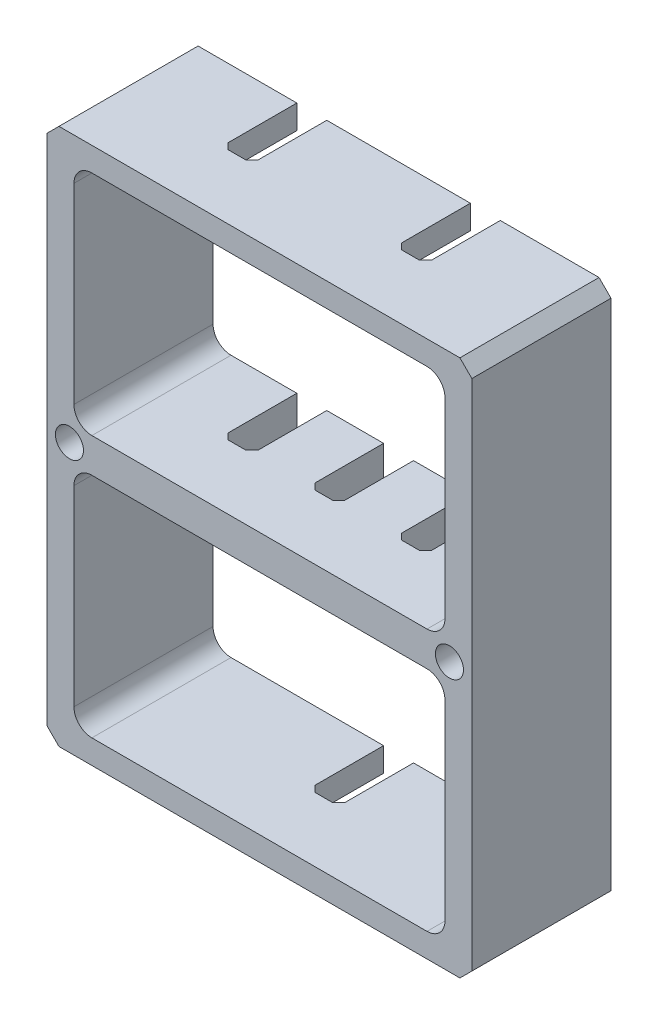
SolidWorks part; units mm, degrees
ref_plane "Front Plane" through (0, 0, 0) normal (0, 0, 1) x (1, 0, 0)
ref_plane "Top Plane" through (0, 0, 0) normal (0, 1, 0) x (1, 0, 0)
ref_plane "Right Plane" through (0, 0, 0) normal (1, 0, 0) x (0, 0, -1)
sketch "Sketch1" plane through (0, 0, 0) normal (0, 0, 1) x (1, 0, 0)
  line L4 (30.226, -70.2945) -> (30.226, -77.9145) construction
  line L5 (15.494, -69.7865) -> (30.226, -69.7865) construction
  line L6 (15.494, -69.7865) -> (15.494, -78.4225) construction
  line L7 (15.494, -78.4225) -> (30.226, -78.4225) construction
  line L8 (10.033, -79.9465) -> (31.877, -79.9465)
  line L9 (31.877, -79.9465) -> (31.877, -64.0516)
  line L10 (35.687, -57.15) -> (13.843, -57.15)
  line L11 (13.843, -57.15) -> (13.843, -73.0449)
  line L12 (13.843, -79.9465) -> (31.877, -79.9465)
  line L13 (31.877, -79.9465) -> (31.877, -57.15)
  line L14 (31.877, -57.15) -> (13.843, -57.15)
  line L15 (13.843, -57.15) -> (13.843, -79.9465)
  line L16 (30.226, -69.7865) -> (30.226, -78.4225) construction
  line L17 (22.86, -78.4225) -> (22.86, -69.7865) construction
  line L18 (15.494, -74.1045) -> (30.226, -74.1045) construction
  line L19 (16.002, -69.7865) -> (29.718, -69.7865) construction
  line L20 (15.494, -77.9145) -> (15.494, -70.2945) construction
  line L21 (29.718, -78.4225) -> (16.002, -78.4225) construction
  line L22 (14.986, -69.2785) -> (30.734, -69.2785)
  line L23 (30.734, -69.2785) -> (30.734, -78.9305)
  line L24 (14.986, -78.9305) -> (30.734, -78.9305)
  line L25 (14.986, -69.2785) -> (14.986, -78.9305)
  line L26 (13.843, -68.5482) -> (31.877, -68.5482) construction
  line L27 (14.986, -67.818) -> (14.986, -58.166)
  line L28 (14.986, -58.166) -> (30.734, -58.166)
  line L29 (30.734, -67.818) -> (30.734, -58.166)
  line L30 (14.986, -67.818) -> (30.734, -67.818)
  line L51 (31.877, -64.0516) -> (35.687, -60.2416)
  line L53 (35.687, -60.2416) -> (35.687, -57.15)
  line L55 (13.843, -73.0449) -> (10.033, -76.8549)
  line L57 (10.033, -76.8549) -> (10.033, -79.9465)
  point P208 (22.86, -74.1045)
  dimension "D2" = 0.508
  dimension "D1" = 0.508
extrude "Boss-Extrude1" add sketch "Sketch1" along normal offset from surface (5.9055 mm away) 1.5875 contours L14 L15 L12 L13 L30 L27 L28 L29 L25 L22 L23 L24
sketch "Sketch2" plane through (0, 0, 0) normal (0, 0, -1) x (-1, 0, 0)
  line L0 (-18.796, -57.404) -> (-19.558, -57.404) construction
  line L3 (-26.162, -57.404) -> (-26.924, -57.404) construction
  line L5 (-23.241, -68.58) -> (-22.479, -68.58) construction
  line L8 (-18.796, -68.5165) -> (-19.558, -68.5165) construction
  line L9 (-26.162, -68.5165) -> (-26.924, -68.5165) construction
  line L10 (-23.241, -79.6925) -> (-22.479, -79.6925) construction
  line L11 (-22.86, -78.9305) -> (-22.86, -79.9465)
  line L12 (-30.734, -78.9305) -> (-14.986, -78.9305) construction
  line L13 (-31.877, -79.9465) -> (-13.843, -79.9465) construction
  line L14 (-19.177, -57.15) -> (-19.177, -58.166)
  line L15 (-13.843, -57.15) -> (-31.877, -57.15) construction
  line L16 (-30.734, -58.166) -> (-14.986, -58.166) construction
  line L17 (-26.543, -57.15) -> (-26.543, -58.166)
  line L18 (-22.86, -69.2785) -> (-22.86, -67.818)
  line L19 (-30.734, -69.2785) -> (-14.986, -69.2785) construction
  line L20 (-30.734, -67.818) -> (-14.986, -67.818) construction
  line L21 (-19.177, -69.2785) -> (-19.177, -67.818)
  line L22 (-26.543, -69.2785) -> (-26.543, -67.818)
  point P0 (-19.177, -57.404)
  point P1 (-26.543, -57.404)
  point P4 (-22.86, -68.58)
  point P7 (-19.177, -68.5165)
  point P10 (-26.543, -68.5165)
  point P13 (-22.86, -79.6925)
extrude "Cut-Extrude-Thin2" cut sketch "Sketch2" against normal blind 3.175 thin contours L14 | L17 | L21 | L18 | L22 | L11 thin type mid plane wall 1.27
chamfer "Chamfer1" distance 0.254 angle 45 12 edges at (23.495, -79.4385, 3.175) (22.225, -79.4385, 3.175) (27.178, -68.5482, 3.175) (25.908, -68.5482, 3.175) (22.225, -68.5482, 3.175) (23.495, -68.5482, 3.175) (19.812, -68.5482, 3.175) (18.542, -68.5482, 3.175) (18.542, -57.658, 3.175) (19.812, -57.658, 3.175) (25.908, -57.658, 3.175) (27.178, -57.658, 3.175)
chamfer "Chamfer2" distance 0.508 angle 45 4 edges at (31.877, -57.15, 2.9527) (13.843, -57.15, 2.9528) (13.843, -79.9465, 2.9528) (31.877, -79.9465, 2.9528)
fillet "Fillet1" radius 0.762 8 edges at (14.986, -78.9305, 2.9528) (30.734, -78.9305, 2.9528) (30.734, -69.2785, 2.9528) (14.986, -69.2785, 2.9528) (14.986, -67.818, 2.9528) (30.734, -67.818, 2.9528) (14.986, -58.166, 2.9528) (30.734, -58.166, 2.9528)
hole_wizard "#0-80 Tapped Hole1" positions "Sketch4" profile "Sketch3" tap size "#0-80" standard "ANSI Inch" end condition through all
sketch "Sketch4" plane through (0, 0, 0) normal (0, 0, -1) x (-1, 0, 0)
  line L0 (-15.748, -69.2785) -> (-15.748, -67.818) construction
  line L2 (-15.748, -68.5482) -> (-13.843, -68.5482) construction
  line L3 (-13.843, -57.658) -> (-13.843, -79.4385) construction
  line L5 (-22.86, -57.15) -> (-22.86, -79.9465) construction
  line L6 (-25.908, -57.15) -> (-19.812, -57.15) construction
  line L7 (-22.479, -79.9465) -> (-23.241, -79.9465) construction
  point P12 (-14.7955, -68.5482)
  point P25 (-30.9245, -68.5482)
sketch "Sketch3" plane through (14.7955, -68.5482, 0) normal (1, 0, 0) x (0, 1, 0)
  line L0 (0, 0) -> (0, 5.9055)
  line L1 (0, 5.9055) -> (0.5956, 5.9055)
  line L2 (0.5956, 5.9055) -> (0.5956, 0)
  line L5 (0.5956, 0) -> (0, 0)
  line L11 (0, -6.35) -> (0, 107.95) construction
  dimension "Thru Tap Drill Dia." = 1.1913
  dimension "Thru Tap Drill Depth" = 5.9055
cosmetic thread "Hole Thread1" parameters "D2"=1.524
cosmetic thread "Hole Thread2" parameters "D2"=1.524
